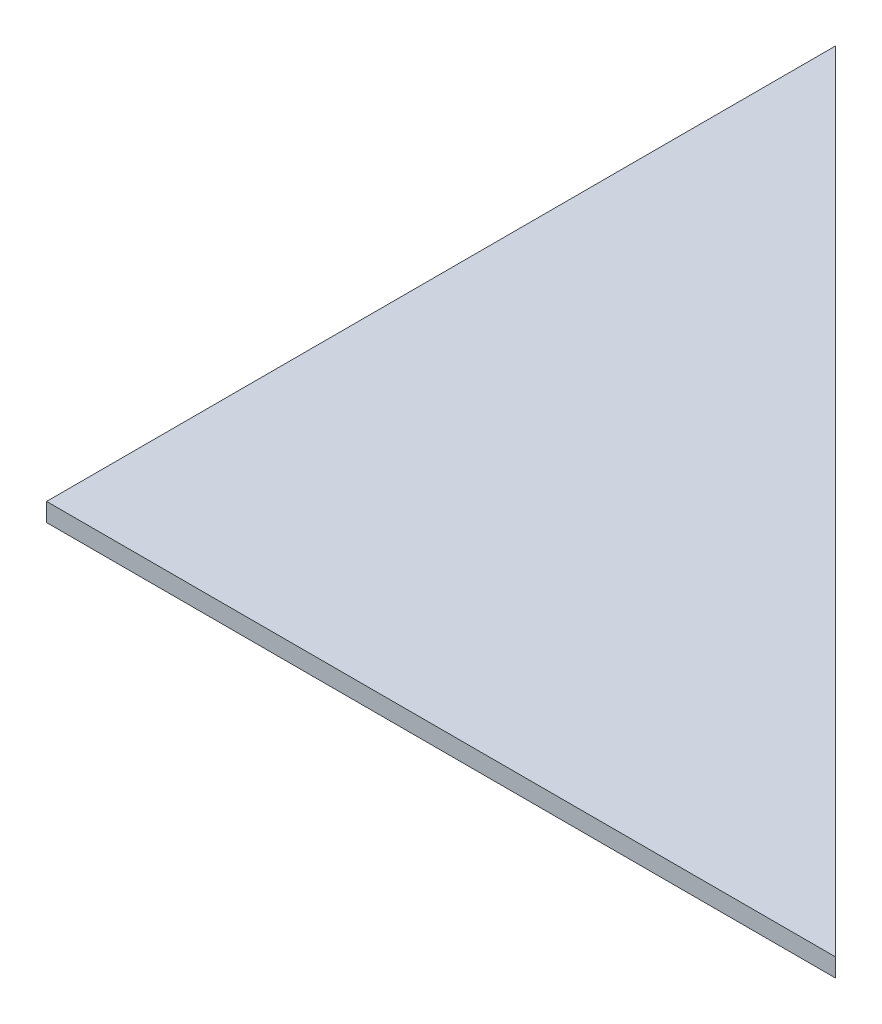
SolidWorks part; units mm, degrees
ref_plane "前视基准面" through (0, 0, 0) normal (0, 0, 1) x (1, 0, 0)
ref_plane "上视基准面" through (0, 0, 0) normal (0, 1, 0) x (1, 0, 0)
ref_plane "右视基准面" through (0, 0, 0) normal (1, 0, 0) x (0, 0, -1)
sketch "草图1" plane through (0, 0, 0) normal (0, 1, 0) x (1, 0, 0)
  line L0 (0, 0) -> (0, 215)
  line L1 (0, 0) -> (215, 0)
  line L2 (0, 215) -> (215, 0)
  dimension "D1" = 215
extrude "凸台-拉伸1" add sketch "草图1" along normal blind 5
